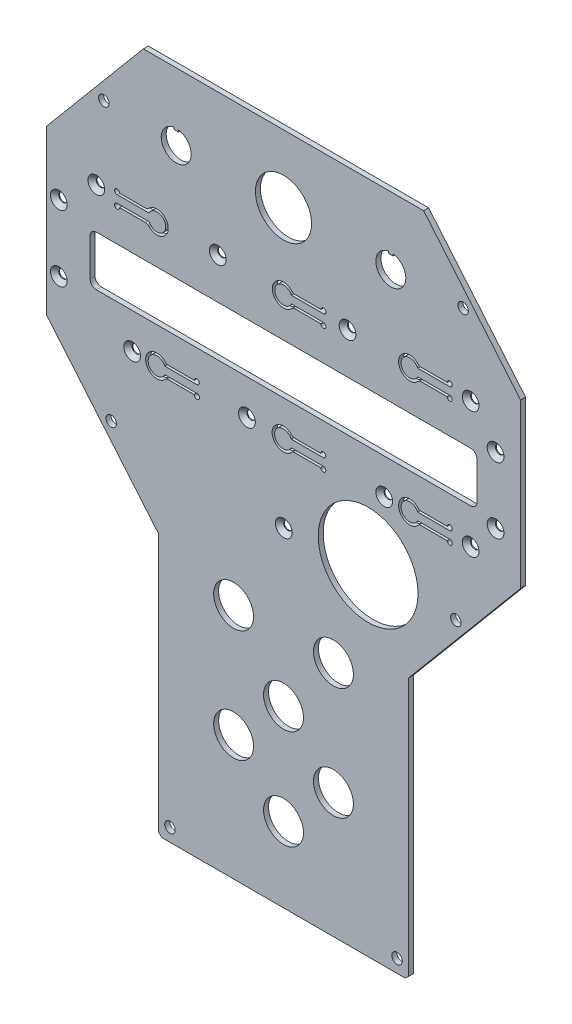
SolidWorks part; units mm, degrees
ref_plane "Plano frontal" through (0, 0, 0) normal (0, 0, 1) x (1, 0, 0)
ref_plane "Plano superior" through (0, 0, 0) normal (0, 1, 0) x (1, 0, 0)
ref_plane "Plano direito" through (0, 0, 0) normal (1, 0, 0) x (0, 0, -1)
sketch "Esboço1" plane through (0, 0, 0) normal (0, 0, 1) x (1, 0, 0)
  line L6 (55.321, 133.8096) -> (-57.007, 133.8096)
  line L7 (-57.007, 133.8096) -> (-95.843, 87.5267)
  line L8 (-95.843, 87.5267) -> (-95.843, 22.1402)
  line L9 (-95.843, 22.1402) -> (-50.843, -31.4887)
  line L10 (-50.843, -31.4887) -> (-50.843, -135.0827)
  line L11 (-50.843, -135.0827) -> (-49.5229, -136.1904)
  line L12 (-49.5229, -136.1904) -> (47.8369, -136.1904)
  line L13 (49.157, -135.0827) -> (47.8369, -136.1904)
  line L14 (49.157, -31.4887) -> (49.157, -135.0827)
  line L15 (94.157, 22.1402) -> (49.157, -31.4887)
  line L16 (94.157, 87.5267) -> (94.157, 22.1402)
  line L17 (55.321, 133.8096) -> (94.157, 87.5267)
  point P16 (-0.843, -136.1904)
  point P17 (-0.843, 133.8096)
  dimension "D2" = 140
  dimension "AberturaSuperior" = 140
extrude "Ressalto-extrusão1" add sketch "Esboço1" along normal blind 2
sketch "Esboço2" plane through (0, 0, 2) normal (0, 0, 1) x (1, 0, 0)
  line L0 (-0.843, -146.6722) -> (-0.843, 180.0647) construction
  line L1 (-95.843, 87.5267) -> (-95.843, 22.1402) construction
  line L2 (55.321, 133.8096) -> (-57.007, 133.8096) construction
  line L3 (-95.843, 22.1402) -> (-50.843, -31.4887) construction
  line L6 (49.157, -135.0827) -> (49.157, -31.4887) construction
  line L7 (-49.5229, -136.1904) -> (47.8369, -136.1904) construction
  line L9 (-50.843, -31.4887) -> (-50.843, -135.0827) construction
  circle A0 centre (-72.8144, 107.9499) radius 2.1
  circle A1 centre (-46.343, -130.9644) radius 2.1
  circle A2 centre (44.657, -130.9644) radius 2.1
  circle A3 centre (71.1284, 107.9499) radius 2.1
  circle A4 centre (-69.8958, -1.7817) radius 2.1
  circle A5 centre (68.2098, -1.7817) radius 2.1
  dimension "D1" = 23.0286
  dimension "D2" = 4.5
  dimension "D3" = 4.5
  dimension "D7" = 25.8597
  dimension "D4" = 5.226
  dimension "D11" = 4.5
extrude "Corte-extrusão1" cut sketch "Esboço2" against normal up to next
sketch "Esboço3" plane through (0, 0, 2) normal (0, 0, 1) x (1, 0, 0)
  line L0 (-95.843, 87.5267) -> (-95.843, 22.1402) construction
  line L1 (-49.5229, -136.1904) -> (47.8369, -136.1904) construction
  line L2 (-75.843, 40.8096) -> (74.157, 40.8096)
  line L3 (-78.343, 43.3096) -> (-78.343, 58.3096)
  line L4 (-75.843, 60.8096) -> (74.157, 60.8096)
  line L5 (76.657, 43.3096) -> (76.657, 58.3096)
  line L6 (-78.343, 40.8096) -> (76.657, 60.8096) construction
  line L7 (-78.343, 60.8096) -> (76.657, 40.8096) construction
  arc A0 (74.157, 60.8096) -> (76.657, 58.3096) centre (74.157, 58.3096) cw
  arc A1 (74.157, 40.8096) -> (76.657, 43.3096) centre (74.157, 43.3096) ccw
  arc A2 (-75.843, 40.8096) -> (-78.343, 43.3096) centre (-75.843, 43.3096) cw
  arc A3 (-78.343, 58.3096) -> (-75.843, 60.8096) centre (-75.843, 58.3096) cw
  dimension "D1" = 2.5
  dimension "D2" = 155
  dimension "D3" = 20
  dimension "D4" = 17.5
  dimension "D5" = 177
extrude "Corte-extrusão2" cut sketch "Esboço3" against normal up to next
sketch "Esboço4" plane through (0, 0, 2) normal (0, 0, 1) x (1, 0, 0)
  line L2 (-49.5229, -136.1904) -> (47.8369, -136.1904) construction
  line L3 (94.157, 22.1402) -> (94.157, 87.5267) construction
  circle A0 centre (33.0563, -0.1904) radius 20
  dimension "D1" = 136
  dimension "D2" = 61.1007
extrude "Corte-extrusão3" cut sketch "Esboço4" against normal up to next
sketch "Esboço5" plane through (0, 0, 2) normal (0, 0, 1) x (1, 0, 0)
  line L0 (-0.843, -66.1904) -> (-0.843, -106.1904) construction
  line L1 (-50.843, -31.4887) -> (-50.843, -135.0827) construction
  line L2 (55.321, 133.8096) -> (-57.007, 133.8096) construction
  line L3 (-44.743, 112.7417) -> (-44.743, 111.9417)
  line L4 (-44.743, 111.9417) -> (-42.943, 111.9417)
  line L5 (-42.943, 111.9417) -> (-42.943, 112.7417)
  line L6 (41.257, 112.7417) -> (41.257, 111.9417)
  line L7 (41.257, 111.9417) -> (43.057, 111.9417)
  line L8 (43.057, 111.9417) -> (43.057, 112.7417)
  line L9 (-20.843, -41.1904) -> (19.157, -41.1904) construction
  line L10 (-49.5229, -136.1904) -> (47.8369, -136.1904) construction
  line L11 (-50.843, -56.8553) -> (49.157, -56.8553) construction
  line L12 (49.157, -135.0827) -> (49.157, -31.4887) construction
  circle A0 centre (-20.843, -86.1904) radius 8
  circle A1 centre (19.157, -86.1904) radius 8
  circle A2 centre (-0.843, -106.1904) radius 8
  circle A3 centre (-0.843, -66.1904) radius 8
  circle A4 centre (-20.843, -41.1904) radius 8
  circle A5 centre (19.157, -41.1904) radius 8
  circle A6 centre (-0.843, 106.8096) radius 11.25
  arc A7 (-44.743, 112.7417) -> (-42.943, 112.7417) centre (-43.843, 106.8096) ccw
  arc A8 (41.257, 112.7417) -> (43.057, 112.7417) centre (42.157, 106.8096) ccw
  point P1 (-0.843, -41.1904)
  point P3 (-20.843, -41.1904)
  point P10 (-0.843, -56.8553)
  point P32 (-0.843, -86.1904)
  dimension "D14" = 22.5
  dimension "D15" = 12
  dimension "D16" = 12
  dimension "D11" = 27
  dimension "D12" = 43
  dimension "D13" = 43
  dimension "D18" = 1.8
  dimension "D19" = 0.9
  dimension "D20" = 0.8
  dimension "D21" = 1.8
  dimension "D22" = 0.9
  dimension "D23" = 0.8
  dimension "D3" = 40
  dimension "D5" = 45
  dimension "D6" = 40
  dimension "D4" = 50
extrude "Corte-extrusão4" cut sketch "Esboço5" against normal up to next
sketch "Esboço10" plane through (0, 0, 2) normal (0, 0, 1) x (1, 0, 0)
  line L3 (94.157, 22.1402) -> (94.157, 87.5267) construction
  line L4 (74.157, 60.8096) -> (-75.843, 60.8096) construction
  circle A0 centre (-61.4827, 26.6206) radius 1.75
  circle A1 centre (-15.4827, 26.6206) radius 1.75
  circle A2 centre (39.5173, 26.6206) radius 1.75
  circle A3 centre (84.131, 37.971) radius 1.6
  circle A4 centre (84.131, 64.471) radius 1.6
  circle A5 centre (-90.869, 64.471) radius 1.6
  circle A6 centre (-90.869, 37.971) radius 1.6
  circle A7 centre (-27.183, 77.1996) radius 1.75
  circle A8 centre (24.817, 77.1996) radius 1.75
  circle A9 centre (-0.7327, -4.3294) radius 2
  dimension "D1" = 69.3401
  dimension "D2" = 16.39
  dimension "D3" = 52
  dimension "D4" = 30.95
  dimension "D5" = 14.75
hole_wizard "Escareado para parafuso Allen sextavado escareado de M32" positions "3DSketch3" profile "Esboço11" countersink size "M3" standard "ISO" end condition through all
sketch3d "3DSketch3"
  point P0 (-90.869, 64.471, 2)
  point P3 (-90.869, 37.971, 2)
  point P6 (-61.4827, 26.6206, 2)
  point P9 (-15.4827, 26.6206, 2)
  point P12 (39.5173, 26.6206, 2)
  point P15 (84.131, 37.971, 2)
  point P18 (84.131, 64.471, 2)
  point P21 (24.817, 77.1996, 2)
  point P24 (-27.183, 77.1996, 2)
  point P32 (-0.7327, -4.3294, 2)
sketch "Esboço11" plane through (-90.869, 64.471, 2) normal (1, 0, 0) x (0, -1, 0)
  line L0 (0, 0) -> (0, 2)
  line L1 (0, 2) -> (1.7, 2)
  line L2 (1.7, 2) -> (1.7, 1.66)
  line L3 (1.7, 1.66) -> (3.36, 0)
  line L5 (3.36, 0) -> (0, 0)
  line L6 (-1.7, 1.66) -> (-3.36, 0) construction
  line L11 (0, -6.35) -> (0, 107.95) construction
  dimension "Thru Hole Dia." = 3.4
  dimension "Thru Hole Depth" = 2
  dimension "Near C'Sink Dia." = 6.72
  dimension "Near C'Sink Angle" = 90
sketch "Esboço12" plane through (0, 0, 2) normal (0, 0, 1) x (1, 0, 0)
  line L0 (-75.843, 40.8096) -> (74.157, 40.8096) construction
  line L1 (74.157, 60.8096) -> (-75.843, 60.8096) construction
  line L2 (94.157, 22.1402) -> (94.157, 87.5267) construction
  line L3 (52.9293, 28.0196) -> (65.767, 28.0196)
  line L5 (64.767, 29.0196) -> (53.5087, 29.0196)
  line L6 (52.9293, 25.0196) -> (65.767, 25.0196)
  line L7 (2.2593, 28.0196) -> (15.097, 28.0196)
  line L8 (64.767, 24.0196) -> (53.5087, 24.0196)
  line L9 (14.097, 24.0196) -> (2.8387, 24.0196)
  line L10 (14.097, 29.0196) -> (2.8387, 29.0196)
  line L11 (2.2593, 25.0196) -> (15.097, 25.0196)
  line L12 (-48.4107, 28.0196) -> (-35.573, 28.0196)
  line L13 (-36.6534, 24.0196) -> (-47.8313, 24.0196)
  line L14 (-36.573, 29.0196) -> (-47.8313, 29.0196)
  line L15 (-48.4107, 25.0196) -> (-35.9821, 25.0196)
  line L25 (2.3293, 77.9796) -> (15.167, 77.9796)
  line L26 (52.9293, 77.9796) -> (65.767, 77.9796)
  line L27 (14.167, 78.9796) -> (2.9087, 78.9796)
  line L28 (2.3293, 74.9796) -> (15.167, 74.9796)
  line L29 (-54.6953, 77.9796) -> (-67.533, 77.9796)
  line L30 (14.167, 73.9796) -> (2.9087, 73.9796)
  line L31 (64.767, 78.9796) -> (53.5087, 78.9796)
  line L32 (52.9293, 74.9796) -> (65.767, 74.9796)
  line L34 (64.767, 73.9796) -> (53.5087, 73.9796)
  line L35 (-66.533, 78.9796) -> (-55.2746, 78.9796)
  line L36 (-54.6953, 74.9796) -> (-67.533, 74.9796)
  line L38 (-66.533, 73.9796) -> (-55.2746, 73.9796)
  arc A0 (53.5087, 29.0196) -> (53.5087, 24.0196) centre (49.767, 26.5196) ccw
  arc A2 (15.097, 25.0196) -> (14.097, 24.0196) centre (15.097, 24.0196) cw
  arc A3 (-47.8313, 29.0196) -> (-47.8313, 24.0196) centre (-51.573, 26.5196) ccw
  arc A4 (-55.2746, 73.9796) -> (-55.2746, 78.9796) centre (-51.533, 76.4796) ccw
  arc A5 (2.9087, 78.9796) -> (2.9087, 73.9796) centre (-0.833, 76.4796) ccw
  arc A6 (53.5087, 78.9796) -> (53.5087, 73.9796) centre (49.767, 76.4796) ccw
  arc A7 (52.9293, 28.0196) -> (52.9293, 25.0196) centre (49.767, 26.5196) ccw
  arc A8 (65.767, 28.0196) -> (64.767, 29.0196) centre (65.767, 29.0196) ccw
  arc A9 (64.767, 24.0196) -> (65.767, 25.0196) centre (65.767, 24.0196) ccw
  arc A10 (15.097, 28.0196) -> (14.097, 29.0196) centre (15.097, 29.0196) ccw
  arc A11 (2.8387, 29.0196) -> (2.8387, 24.0196) centre (-0.903, 26.5196) ccw
  arc A12 (2.2593, 28.0196) -> (2.2593, 25.0196) centre (-0.903, 26.5196) ccw
  arc A13 (-35.573, 28.0196) -> (-36.573, 29.0196) centre (-35.573, 29.0196) ccw
  arc A14 (-35.9821, 25.0196) -> (-36.6534, 24.0196) centre (-35.573, 24.0196) cw
  arc A17 (-48.4107, 28.0196) -> (-48.4107, 25.0196) centre (-51.573, 26.5196) ccw
  arc A22 (15.167, 77.9796) -> (14.167, 78.9796) centre (15.167, 78.9796) ccw
  arc A23 (52.9293, 77.9796) -> (52.9293, 74.9796) centre (49.767, 76.4796) ccw
  arc A24 (2.3293, 77.9796) -> (2.3293, 74.9796) centre (-0.833, 76.4796) ccw
  arc A25 (14.167, 73.9796) -> (15.167, 74.9796) centre (15.167, 73.9796) ccw
  arc A26 (65.767, 77.9796) -> (64.767, 78.9796) centre (65.767, 78.9796) ccw
  arc A27 (64.767, 73.9796) -> (65.767, 74.9796) centre (65.767, 73.9796) ccw
  arc A28 (-54.6953, 74.9796) -> (-54.6953, 77.9796) centre (-51.533, 76.4796) ccw
  arc A29 (-66.533, 78.9796) -> (-67.533, 77.9796) centre (-67.533, 78.9796) ccw
  arc A30 (-67.533, 74.9796) -> (-66.533, 73.9796) centre (-67.533, 73.9796) ccw
  dimension "D2" = 14.29
  dimension "D5" = 15.67
  dimension "D6" = 44.39
  dimension "D7" = 50.6
  dimension "D8" = 50.7
  dimension "D9" = 1
  dimension "D13" = 16
  dimension "D14" = 4.5
  dimension "D15" = 3.5
  dimension "D16" = 3.5
  dimension "D17" = 4.5
  dimension "D10" = 1
  dimension "D18" = 16
  dimension "D22" = 3.5
  dimension "D19" = 44.39
  dimension "D33" = 4.5
  dimension "D38" = 4.5
  dimension "D42" = 1
  dimension "D39" = 3.5
  dimension "D44" = 16
  dimension "D46" = 4.5
  dimension "D47" = 3.5
  dimension "D45" = 16
  dimension "D50" = 4.5
  dimension "D51" = 3.5
  dimension "D52" = 16
  dimension "D21" = 50.67
  dimension "D11" = 3
  dimension "D12" = 1.5
  dimension "D20" = 50.67
  dimension "D23" = 16
  dimension "D40" = 3
  dimension "D41" = 1.5
  dimension "D43" = 1
extrude "Corte-extrusão5" cut sketch "Esboço12" against normal blind 10
fillet "Filete1" radius 2 11 edges at (-47.8313, 24.0196, 1) (2.8387, 24.0196, 1) (53.5087, 73.9796, 1) (-47.8313, 29.0196, 1) (2.8387, 29.0196, 1) (53.5087, 29.0196, 1) (53.5087, 78.9796, 1) (2.9087, 73.9796, 1) (2.9087, 78.9796, 1) (-55.2746, 73.9796, 1) (-55.2746, 78.9796, 1)
sketch "Esboço13" plane through (0, 0, 2) normal (0, 0, 1) x (1, 0, 0)
  line L0 (74.157, 60.8096) -> (-75.843, 60.8096) construction
  line L1 (-95.843, 87.5267) -> (-95.843, 22.1402) construction
  line L2 (94.157, 22.1402) -> (94.157, 87.5267) construction
  circle A0 centre (-75.843, 77.1996) radius 2
  circle A1 centre (74.157, 77.1996) radius 2
  circle A9 centre (74.157, 26.6206) radius 2
  circle A10 centre (39.5173, 26.6206) radius 1.7 construction
  dimension "D1" = 16.39
  dimension "D3" = 20
  dimension "D4" = 0
  dimension "D5" = 20
  dimension "D2" = 20
hole_wizard "Escareado para parafuso Allen sextavado escareado de M33" positions "3DSketch4" profile "Esboço14" countersink size "M3" standard "ISO" end condition through all
sketch3d "3DSketch4"
  point P0 (-75.843, 77.1996, 2)
  point P3 (74.157, 77.1996, 2)
  point P6 (74.157, 26.6206, 2)
sketch "Esboço14" plane through (-75.843, 77.1996, 2) normal (1, 0, 0) x (0, -1, 0)
  line L0 (0, 0) -> (0, 2)
  line L1 (0, 2) -> (1.7, 2)
  line L2 (1.7, 2) -> (1.7, 1.66)
  line L3 (1.7, 1.66) -> (3.36, 0)
  line L5 (3.36, 0) -> (0, 0)
  line L6 (-1.7, 1.66) -> (-3.36, 0) construction
  line L11 (0, -6.35) -> (0, 107.95) construction
  dimension "Thru Hole Dia." = 3.4
  dimension "Thru Hole Depth" = 2
  dimension "Near C'Sink Dia." = 6.72
  dimension "Near C'Sink Angle" = 90
equation "\"offsetY\"= 40"
equation "\"D3@Esboço5\"=\"offsetY\""
equation "\"offsetZ\"= 45"
equation "\"offsetButtonZ\"= 40"
equation "\"zInicial\"= 50"
equation "\"D5@Esboço5\"=\"offsetZ\""
equation "\"D4@Esboço5\"=\"zInicial\""
equation "\"D6@Esboço5\"=\"offsetButtonZ\""
